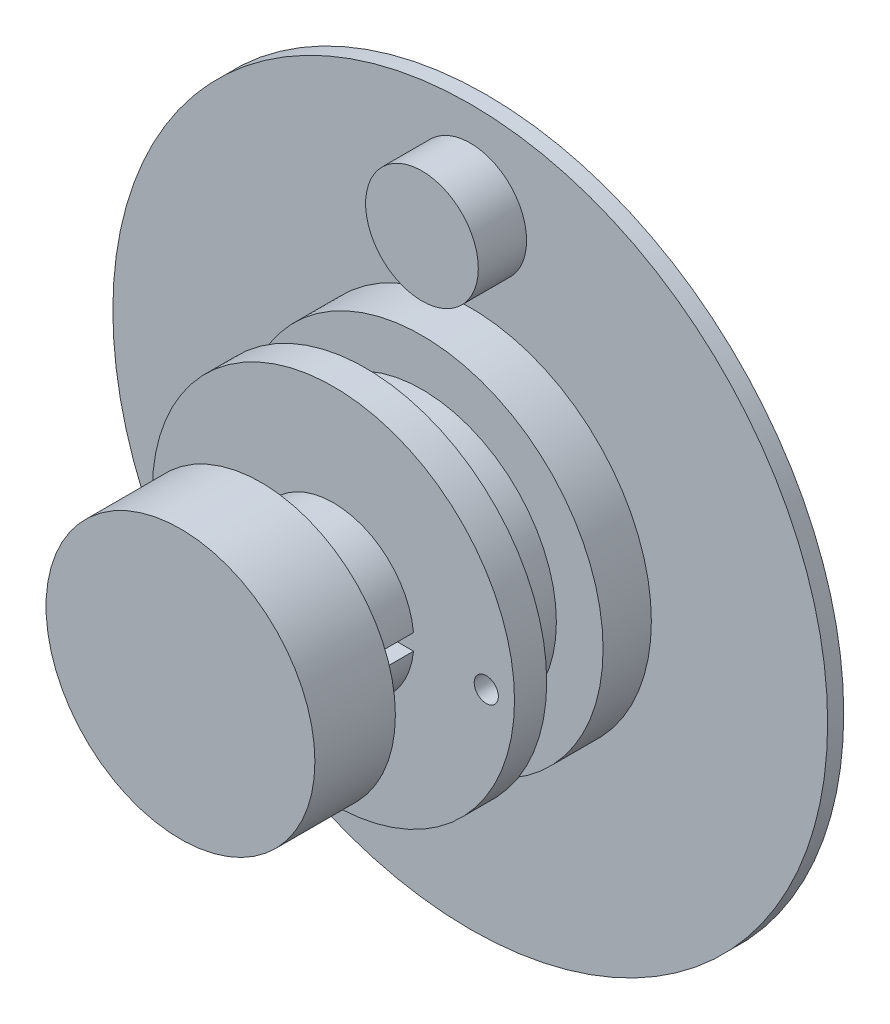
SolidWorks part; units mm, degrees
material "Thornel Mat VMA"
ref_plane "Front Plane" through (0, 0, 0) normal (0, 0, 1) x (1, 0, 0)
ref_plane "Top Plane" through (0, 0, 0) normal (0, 1, 0) x (1, 0, 0)
ref_plane "Right Plane" through (0, 0, 0) normal (1, 0, 0) x (0, 0, -1)
sketch "Sketch1" plane through (0, 0, 0) normal (0, 0, 1) x (1, 0, 0)
  circle A0 centre (0, 0) radius 22.2
  dimension "D2" = 44.4
extrude "Boss-Extrude1" add sketch "Sketch1" along normal blind 1
sketch "Sketch2" plane through (0, 0, 0) normal (0, 0, 1) x (1, 0, 0)
  circle A3 centre (0, 0) radius 11.25
extrude "Boss-Extrude2" add sketch "Sketch2" along normal blind 8.5 from surface at 1 starting at face at (22.2, 0, 1)
sketch "Sketch3" plane through (0, 0, 0) normal (0, 0, 1) x (1, 0, 0)
  circle A0 centre (0, 0) radius 5
  dimension "D1" = 10
extrude "Boss-Extrude3" add sketch "Sketch3" along normal blind 9.5 from surface at 9.5 starting at face at (11.25, 0, 9.5)
sketch "Sketch4" plane through (0, 0, 0) normal (0, 0, 1) x (1, 0, 0)
  line L1 (-5.8109, -0.5) -> (5.8109, -0.5)
  line L2 (-5.8109, -0.5) -> (-5.8109, 0.5)
  line L3 (-5.8109, 0.5) -> (5.8109, 0.5)
  line L4 (5.8109, -0.5) -> (5.8109, 0.5)
  line L5 (-5.8109, -0.5) -> (5.8109, 0.5) construction
  line L6 (-5.8109, 0.5) -> (5.8109, -0.5) construction
  point P0 (0, 0)
  dimension "D1" = 1
extrude "Cut-Extrude1" cut sketch "Sketch4" against normal up to surface (9.5 mm away) from surface at 19 up to face at (5, 0, 9.5) starting at face at (5, 0, 19)
sketch "Sketch5" plane through (0, 0, 0) normal (0, 0, 1) x (1, 0, 0)
  circle A0 centre (0, 16.6) radius 3.5
  dimension "D2" = 7
  dimension "D1" = 16.6
extrude "Boss-Extrude4" add sketch "Sketch5" along normal blind 3 from surface at 1 starting at face at (11.25, 0, 1)
sketch "Sketch6" plane through (0, 0, 0) normal (0, 0, -1) x (-1, 0, 0)
  circle A0 centre (0, 0) radius 6
extrude "Cut-Extrude2" cut sketch "Sketch6" against normal blind 3.5
sketch "Sketch8" plane through (0, 0, 9.5) normal (0, 0, 1) x (1, 0, 0)
  circle A2 centre (0, 0) radius 11.25
  circle A3 centre (0, 0) radius 4
extrude "Cut-Extrude6" [suppressed] cut sketch "Sketch8" against normal blind 3
sketch "Sketch9" plane through (0, 0, 19) normal (0, 0, 1) x (1, 0, 0)
  circle A0 centre (0, 0) radius 8.35
extrude "Boss-Extrude5" add sketch "Sketch9" against normal blind 5
sketch "Sketch10" plane through (0, 0, 9.5) normal (0, 0, 1) x (1, 0, 0)
  circle A0 centre (0, 0) radius 8.35 construction
  circle A1 centre (0, 0) radius 8.35
  circle A2 centre (0, 0) radius 11.25 construction
  circle A3 centre (0, 0) radius 11.25
extrude "Cut-Extrude7" cut sketch "Sketch10" against normal blind 3.5 from offset 2 offset against normal yes
sketch "Sketch11" plane through (0, 0, 9.5) normal (0, 0, 1) x (1, 0, 0)
  line L0 (0, 0) -> (9.4951, -0.3047) construction
  circle A0 centre (9.4951, -0.3047) radius 0.75
extrude "Cut-Extrude8" cut sketch "Sketch11" against normal blind 3
